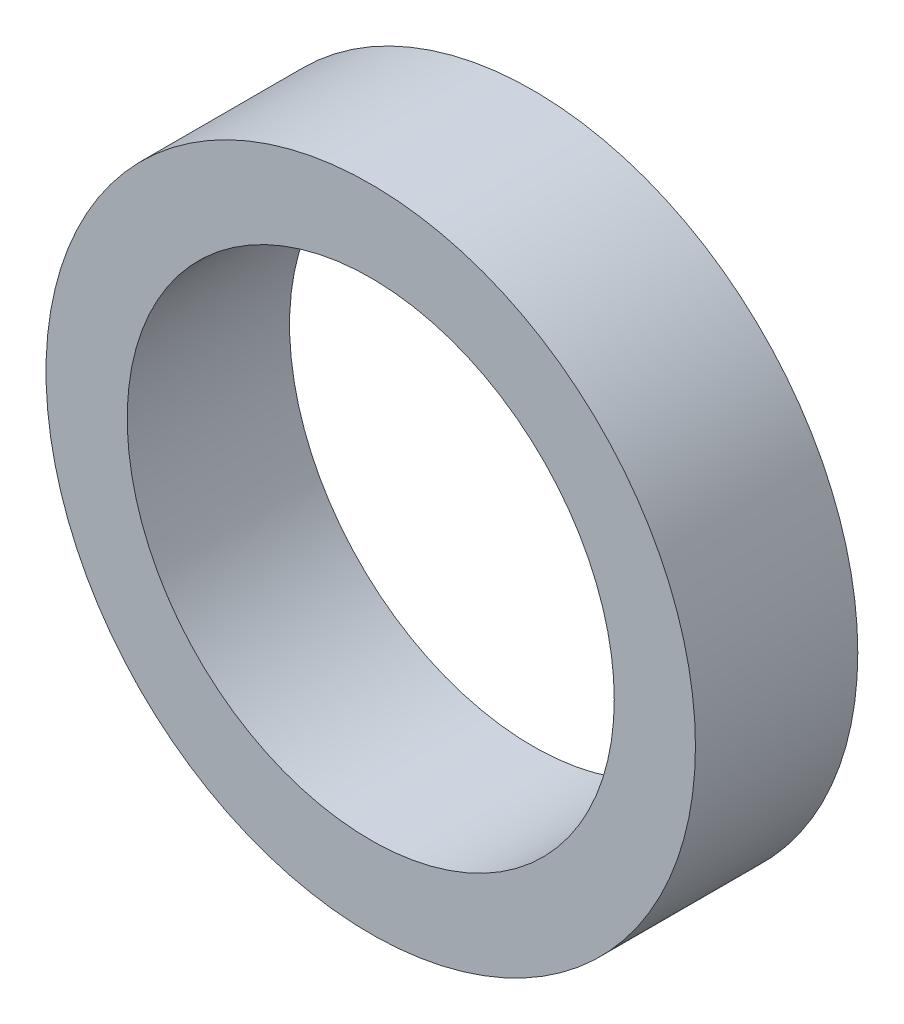
SolidWorks part; units mm, degrees
ref_plane "Front Plane" through (0, 0, 0) normal (0, 0, 1) x (1, 0, 0)
ref_plane "Top Plane" through (0, 0, 0) normal (0, 1, 0) x (1, 0, 0)
ref_plane "Right Plane" through (0, 0, 0) normal (1, 0, 0) x (0, 0, -1)
sketch "Sketch1" plane through (0, 0, 0) normal (0, 0, 1) x (1, 0, 0)
  circle A0 centre (0, 0) radius 8
  circle A1 centre (0, 0) radius 6
  dimension "D1" = 16
  dimension "D2" = 12
extrude "Boss-Extrude1" add sketch "Sketch1" along normal blind 4
